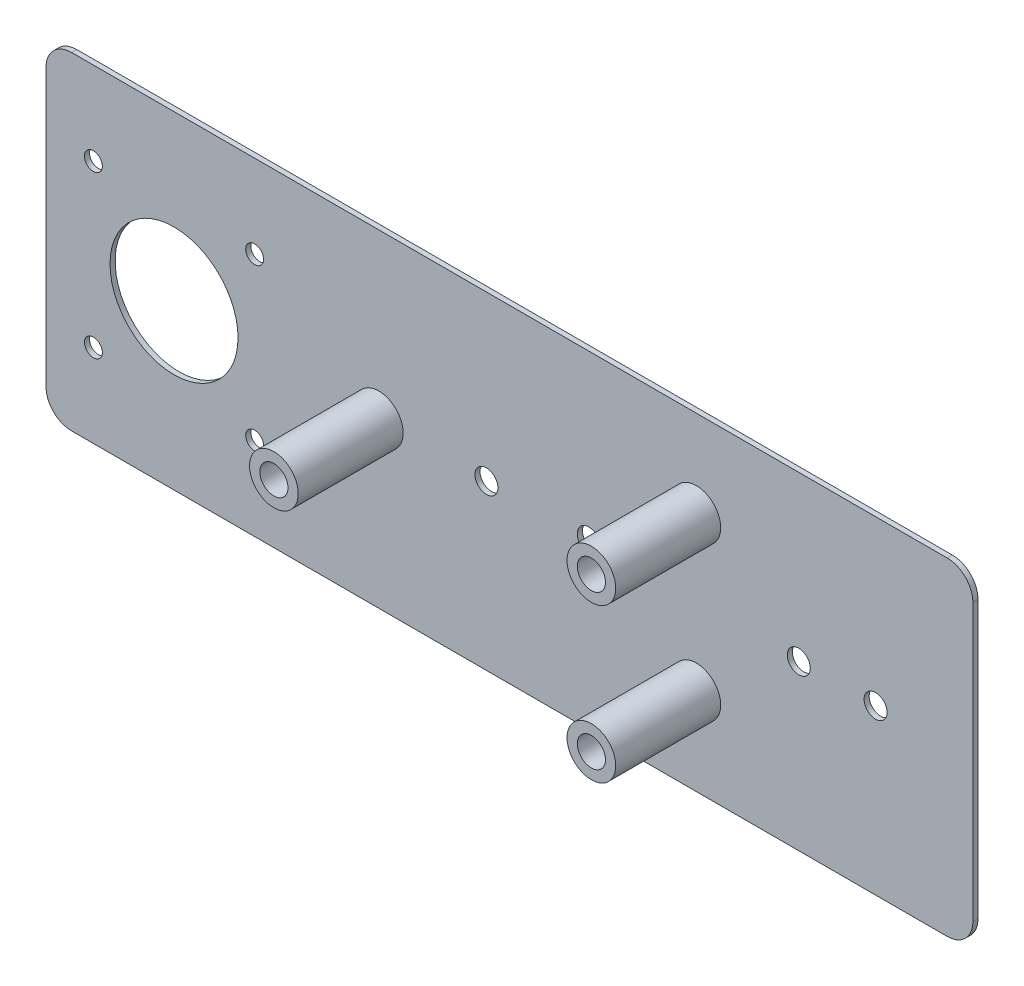
SolidWorks part; units mm, degrees
material "ABS PC"
ref_plane "Front Plane" through (0, 0, 0) normal (0, 0, 1) x (1, 0, 0)
ref_plane "Top Plane" through (0, 0, 0) normal (0, 1, 0) x (1, 0, 0)
ref_plane "Right Plane" through (0, 0, 0) normal (1, 0, 0) x (0, 0, -1)
sketch "Sketch1" plane through (0, 0, 0) normal (0, 0, 1) x (1, 0, 0)
  line L1 (-85.5, 32) -> (85.5, 32)
  line L2 (-90.5, 27) -> (-90.5, -27)
  line L3 (-85.5, -32) -> (85.5, -32)
  line L4 (90.5, 27) -> (90.5, -27)
  line L5 (-90.5, 32) -> (90.5, -32) construction
  line L6 (-90.5, -32) -> (90.5, 32) construction
  arc A0 (85.5, -32) -> (90.5, -27) centre (85.5, -27) ccw
  arc A1 (85.5, 32) -> (90.5, 27) centre (85.5, 27) cw
  arc A2 (-90.5, -27) -> (-85.5, -32) centre (-85.5, -27) ccw
  arc A3 (-85.5, 32) -> (-90.5, 27) centre (-85.5, 27) ccw
  point P0 (0, 0)
  dimension "D3" = 5
  dimension "D1" = 64
  dimension "D2" = 181
extrude "Boss-Extrude1" add sketch "Sketch1" along normal blind 37
sketch "Sketch2" plane through (0, 0, 37) normal (0, 0, 1) x (1, 0, 0)
  line L0 (-65.5, 0) -> (0, 0) construction
  line L1 (-49.75, 15.75) -> (-81.25, 15.75) construction
  line L2 (-49.75, 15.75) -> (-49.75, -15.75) construction
  line L3 (-49.75, -15.75) -> (-81.25, -15.75) construction
  line L4 (-81.25, 15.75) -> (-81.25, -15.75) construction
  line L5 (-49.75, 15.75) -> (-81.25, -15.75) construction
  line L6 (-49.75, -15.75) -> (-81.25, 15.75) construction
  line L7 (-90.5, 27) -> (-90.5, -27) construction
  line L8 (36.5, 15) -> (36.5, -15) construction
  line L9 (0, 0) -> (36.5, 0) construction
  line L10 (36.5, 0) -> (56.5, 0) construction
  circle A0 centre (-81.25, 15.75) radius 1.75
  circle A1 centre (-49.75, 15.75) radius 1.75
  circle A2 centre (-81.25, -15.75) radius 1.75
  circle A3 centre (-49.75, -15.75) radius 1.75
  circle A4 centre (-65.5, 0) radius 12.5
  circle A5 centre (36.5, 15) radius 2.75
  circle A6 centre (36.5, -15) radius 2.75
  circle A7 centre (-25.5, 0) radius 2.75
  circle A8 centre (56.5, 0) radius 2.25
  circle A9 centre (71.5, 0) radius 2.25
  point P0 (-65.5, 0)
  dimension "D1" = 3.5
  dimension "D4" = 25
  dimension "D5" = 5.5
  dimension "D10" = 4.5
  dimension "D11" = 15
  dimension "D2" = 31.5
  dimension "D3" = 25
  dimension "D6" = 30
  dimension "D7" = 127
  dimension "D8" = 62
  dimension "D9" = 20
extrude "Cut-Extrude1" cut sketch "Sketch2" against normal through all
sketch "Sketch3" plane through (0, 0, 37) normal (0, 0, 1) x (1, 0, 0)
  circle A3 centre (36.5, 15) radius 2.75 construction
  circle A4 centre (36.5, 15) radius 2.75
  circle A5 centre (36.5, 15) radius 4.75
  circle A6 centre (-25.5, 0) radius 2.75 construction
  circle A7 centre (36.5, -15) radius 2.75 construction
  circle A8 centre (-25.5, 0) radius 2.75
  circle A9 centre (36.5, -15) radius 2.75
  circle A10 centre (-25.5, 0) radius 4.75
  circle A11 centre (36.5, -15) radius 4.75
  dimension "D1" = 2
  dimension "D2" = 2
sketch "Sketch4" plane through (0, 0, 0) normal (0, 0, 1) x (1, 0, 0)
  line L0 (90.5, 0) -> (90.5, -10) construction
  line L1 (90.5, -27) -> (90.5, 27) construction
  line L2 (0, 0) -> (90.5, 0) construction
  line L3 (90.5, 10) -> (100.5, 10) construction
  line L4 (90.5, -10) -> (100.5, -10) construction
  line L5 (100.5, 2.25) -> (100.5, -2.25) construction
  line L6 (100.5, 10) -> (100.5, 2.25) construction
  line L7 (100.5, -2.25) -> (100.5, -10) construction
  line L8 (90.5, 10) -> (90.5, 0) construction
  arc A0 (100.5, -10) -> (100.5, 10) centre (100.5, 0) ccw construction
  arc A1 (100.5, 2.25) -> (100.5, -2.25) centre (100.5, 0) ccw construction
  arc A2 (100.5, -2.25) -> (100.5, 2.25) centre (100.5, 0) ccw construction
  dimension "D3" = 4.5
  dimension "D1" = 20
  dimension "D2" = 10
sketch "Sketch5" plane through (0, 0, 37) normal (0, 0, 1) x (1, 0, 0)
  line L0 (-25.5, 0) -> (36.5, 0) construction
  line L1 (36.5, 0) -> (36.5, -15) construction
  circle A0 centre (-4.5, 0) radius 2.25
  circle A1 centre (15.5, 0) radius 2.25
  point P10 (5.5, 0)
  dimension "D3" = 4.5
  dimension "D1" = 10
  dimension "D2" = 10
extrude "Cut-Extrude2" cut sketch "Sketch5" against normal through all
sketch "Sketch6" plane through (0, 0, 37) normal (0, 0, 1) x (1, 0, 0)
  line L0 (85.5, 32) -> (-85.5, 32) construction
  line L1 (-85.5, -29) -> (85.5, -29)
  line L2 (-87.5, -27) -> (-87.5, 27)
  line L3 (-85.5, 29) -> (85.5, 29)
  line L4 (87.5, -27) -> (87.5, 27)
  line L5 (-87.5, -29) -> (87.5, 29) construction
  line L6 (-87.5, 29) -> (87.5, -29) construction
  line L7 (90.5, -27) -> (90.5, 27) construction
  arc A0 (-87.5, 27) -> (-85.5, 29) centre (-85.5, 27) cw
  arc A1 (-85.5, -29) -> (-87.5, -27) centre (-85.5, -27) cw
  arc A2 (85.5, -29) -> (87.5, -27) centre (85.5, -27) ccw
  arc A3 (85.5, 29) -> (87.5, 27) centre (85.5, 27) cw
  point P0 (0, 0)
  dimension "D3" = 2
  dimension "D1" = 3
  dimension "D2" = 3
extrude "Cut-Extrude3" cut sketch "Sketch6" against normal blind 36
sketch "Sketch7" plane through (0, 0, 1) normal (0, 0, 1) x (1, 0, 0)
  circle A0 centre (-25.5, 0) radius 4.75
  circle A1 centre (-25.5, 0) radius 2.75 construction
  circle A2 centre (36.5, -15) radius 4.75
  circle A3 centre (36.5, 15) radius 4.75
  circle A4 centre (36.5, -15) radius 2.75 construction
  dimension "D1" = 2
  dimension "D2" = 2
  dimension "D3" = 9.5
extrude "Boss-Extrude2" add sketch "Sketch7" along normal blind 20.5
sketch "Sketch10" plane through (0, 0, 37) normal (0, 0, 1) x (1, 0, 0)
  line L0 (-85.5, -32) -> (85.5, -32) construction
  line L1 (-14.5, -32) -> (25.5, -32)
  line L2 (-14.5, -32) -> (-14.5, 32)
  line L3 (-14.5, 32) -> (25.5, 32)
  line L4 (25.5, -32) -> (25.5, 32)
  line L5 (-14.5, -32) -> (25.5, 32) construction
  line L6 (-14.5, 32) -> (25.5, -32) construction
  line L7 (85.5, 32) -> (-85.5, 32) construction
  line L8 (5.5, 0) -> (36.5, 0) construction
  line L9 (0, 0) -> (90.5, 0) construction
  line L10 (36.5, 0) -> (36.5, -15) construction
  point P0 (5.5, 0)
  dimension "D1" = 40
  dimension "D2" = 31
extrude "Cut-Extrude4" cut sketch "Sketch10" against normal blind 36
sketch "Sketch11" plane through (0, 0, 21.5) normal (0, 0, 1) x (1, 0, 0)
  circle A0 centre (36.5, -15) radius 2.75
  circle A1 centre (-25.5, 0) radius 2.75
  circle A2 centre (36.5, 15) radius 2.75
  dimension "D1" = 5.5
  dimension "D2" = 5.5
  dimension "D3" = 5.5
extrude "Cut-Extrude5" cut sketch "Sketch11" against normal through all
sketch "Sketch12" plane through (0, 0, 1) normal (0, 0, 1) x (1, 0, 0)
  line L0 (25.5, -29) -> (85.5, -29) construction
  line L1 (67.5, -29) -> (82.5, -29)
  line L2 (67.5, -29) -> (67.5, -19)
  line L3 (67.5, -19) -> (82.5, -19)
  line L4 (82.5, -29) -> (82.5, -19)
  line L5 (90.5, 0) -> (32.1507, 0) construction
  line L6 (0, 0) -> (90.5, 0) construction
  line L7 (67.5, 19) -> (82.5, 19)
  line L8 (82.5, 29) -> (82.5, 19)
  line L9 (67.5, 29) -> (82.5, 29)
  line L10 (67.5, 29) -> (67.5, 19)
  line L11 (87.5, -27) -> (87.5, 27) construction
  line L12 (87.5, -6) -> (67.5, -6)
  line L13 (87.5, -6) -> (87.5, -16)
  line L14 (87.5, -16) -> (67.5, -16)
  line L15 (67.5, -6) -> (67.5, -16)
  line L16 (87.5, 16) -> (67.5, 16)
  line L17 (67.5, 6) -> (67.5, 16)
  line L18 (87.5, 6) -> (67.5, 6)
  line L19 (87.5, 6) -> (87.5, 16)
  line L20 (87.5, -27) -> (87.5, 27) construction
  line L21 (-85.5, -29) -> (-14.5, -29) construction
  line L22 (-42.5, -29) -> (-32.5, -29)
  line L23 (-42.5, -29) -> (-42.5, -19)
  line L24 (-42.5, -19) -> (-32.5, -19)
  line L25 (-32.5, -29) -> (-32.5, -19)
  line L26 (-42.5, 19) -> (-32.5, 19)
  line L27 (-32.5, 29) -> (-32.5, 19)
  line L28 (-42.5, 29) -> (-32.5, 29)
  line L29 (-42.5, 29) -> (-42.5, 19)
  line L30 (-87.5, 27) -> (-87.5, -27) construction
  dimension "D1" = 15
  dimension "D2" = 5
  dimension "D3" = 10
  dimension "D4" = 20
  dimension "D5" = 3
  dimension "D6" = 10
  dimension "D7" = 10
  dimension "D8" = 10
  dimension "D9" = 45
extrude "Boss-Extrude3" add sketch "Sketch12" along normal through all
sketch "Sketch14" plane through (0, -16, 0) normal (0, -1, 0) x (1, 0, 0)
  line L3 (87.5, 37) -> (67.5, 37)
  line L4 (67.5, 37) -> (67.5, 3)
  line L5 (67.5, 3) -> (87.5, 37)
  dimension "D1" = 34
extrude "Cut-Extrude6" cut sketch "Sketch14" against normal blind 33
sketch "Sketch16" plane through (82.5, 0, 0) normal (1, 0, 0) x (0, 0, -1)
  line L0 (-37, -19) -> (-3, -19)
  line L1 (-3, -19) -> (-37, -29)
  line L2 (-37, -27) -> (-37, 27) construction
  line L3 (-37, -29) -> (-37, -19)
  dimension "D1" = 10
  dimension "D2" = 34
extrude "Cut-Extrude8" cut sketch "Sketch16" against normal blind 15
sketch "Sketch17" plane through (67.5, 0, 0) normal (-1, 0, 0) x (0, 0, 1)
  line L6 (37, 19) -> (1, 19)
  line L7 (1, 19) -> (37, 29)
  line L8 (37, 29) -> (37, 19)
extrude "Cut-Extrude9" cut sketch "Sketch17" against normal blind 15
sketch "Sketch18" plane through (-32.5, 0, 0) normal (1, 0, 0) x (0, 0, -1)
  line L0 (-37, -29) -> (-37, -19)
  line L1 (-37, -19) -> (-1, -19)
  line L2 (-1, -19) -> (-37, -29)
extrude "Cut-Extrude10" cut sketch "Sketch18" against normal blind 10
sketch "Sketch19" plane through (-32.5, 0, 0) normal (1, 0, 0) x (0, 0, -1)
  line L0 (-37, 29) -> (-1, 19)
  line L1 (-1, 19) -> (-37, 19)
  line L2 (-37, 19) -> (-37, 29)
extrude "Cut-Extrude11" cut sketch "Sketch19" against normal blind 10
sketch "Sketch20" plane through (-90.5, 0, 0) normal (-1, 0, 0) x (0, 0, 1)
  line L0 (37, 27) -> (37, -27) construction
  line L1 (33, 7.5) -> (27, 7.5)
  line L2 (33, 7.5) -> (33, -7.5)
  line L3 (33, -7.5) -> (27, -7.5)
  line L4 (27, 7.5) -> (27, -7.5)
  line L5 (33, 7.5) -> (27, -7.5) construction
  line L6 (33, -7.5) -> (27, 7.5) construction
  line L7 (0, 0) -> (37, 0) construction
  line L8 (37, -2.75) -> (37, 2.75) construction
  point P0 (30, 0)
  dimension "D1" = 4
  dimension "D2" = 15
  dimension "D3" = 6
extrude "Cut-Extrude12" cut sketch "Sketch20" against normal blind 3
sketch "Sketch21" plane through (0, 0, 37) normal (0, 0, 1) x (1, 0, 0)
  line L0 (-90.5, 27) -> (-90.5, -27) construction
  line L1 (-14.5, 32) -> (-90.5, 32)
  line L2 (-14.5, 32) -> (-14.5, -32)
  line L3 (-14.5, -32) -> (-90.5, -32)
  line L4 (-90.5, 32) -> (-90.5, -32)
  line L5 (-85.5, -32) -> (-14.5, -32) construction
  line L6 (90.5, -27) -> (90.5, 27) construction
  line L7 (-30.25, 4.75) -> (-20.75, 4.75)
  line L8 (-30.25, 4.75) -> (-30.25, -4.75)
  line L9 (-30.25, -4.75) -> (-20.75, -4.75)
  line L10 (-20.75, 4.75) -> (-20.75, -4.75)
  line L11 (-30.25, 4.75) -> (-20.75, -4.75) construction
  line L12 (-30.25, -4.75) -> (-20.75, 4.75) construction
  line L13 (25.5, 32) -> (90.5, 32)
  line L14 (25.5, 32) -> (25.5, -32)
  line L15 (25.5, -32) -> (90.5, -32)
  line L16 (90.5, 32) -> (90.5, -32)
  line L17 (25.5, -32) -> (85.5, -32) construction
  line L18 (31.75, -10.25) -> (41.25, -10.25)
  line L19 (31.75, -10.25) -> (31.75, -19.75)
  line L20 (31.75, -19.75) -> (41.25, -19.75)
  line L21 (41.25, -10.25) -> (41.25, -19.75)
  line L22 (31.75, -10.25) -> (41.25, -19.75) construction
  line L23 (31.75, -19.75) -> (41.25, -10.25) construction
  line L24 (31.75, 19.75) -> (41.25, 19.75)
  line L25 (31.75, 19.75) -> (31.75, 10.25)
  line L26 (31.75, 10.25) -> (41.25, 10.25)
  line L27 (41.25, 19.75) -> (41.25, 10.25)
  line L28 (31.75, 19.75) -> (41.25, 10.25) construction
  line L29 (31.75, 10.25) -> (41.25, 19.75) construction
  circle A0 centre (-25.5, 0) radius 4.75 construction
  circle A1 centre (-25.5, 0) radius 4.75 construction
  circle A3 centre (36.5, -15) radius 4.75 construction
  circle A4 centre (36.5, -15) radius 4.75 construction
  circle A5 centre (36.5, 15) radius 4.75 construction
  point P9 (-25.5, 0)
  point P26 (36.5, -15)
  point P32 (36.5, 15)
extrude "Cut-Extrude13" cut sketch "Sketch21" against normal up to surface (36 mm away) up to face at (-30.25, 0, 1)
